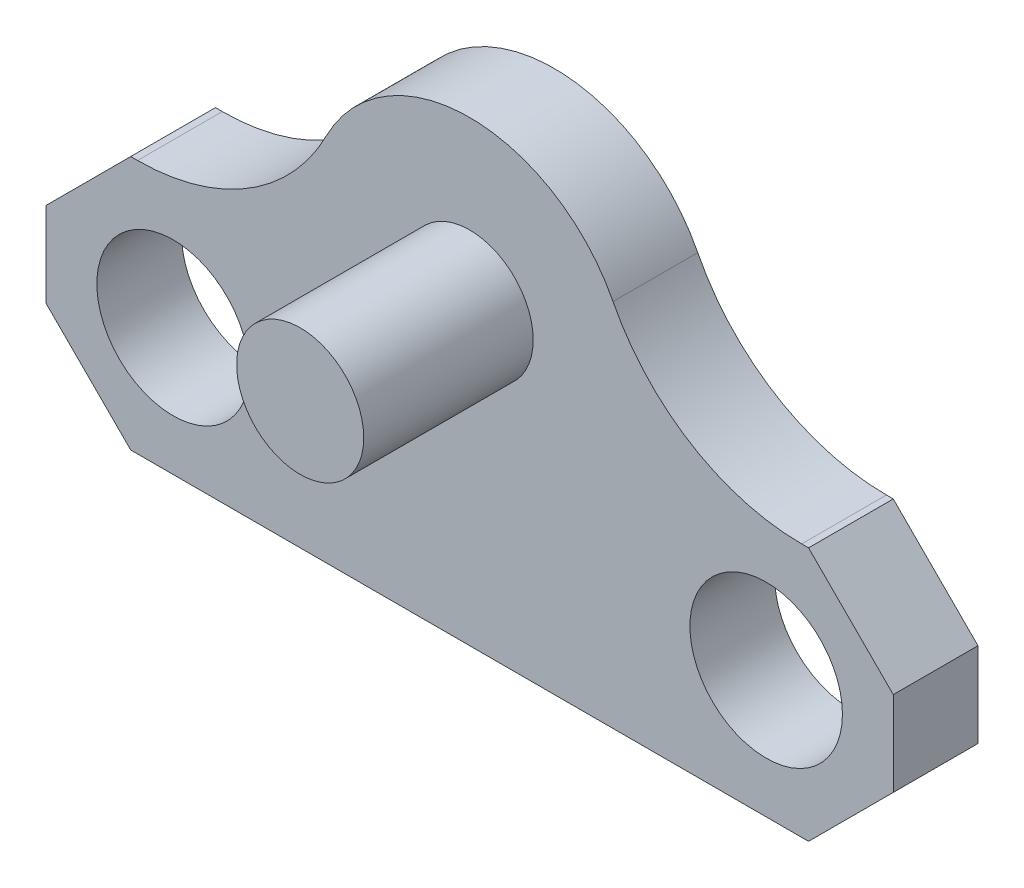
SolidWorks part; units mm, degrees
ref_plane "Front Plane" through (0, 0, 0) normal (0, 0, 1) x (1, 0, 0)
ref_plane "Top Plane" through (0, 0, 0) normal (0, 1, 0) x (1, 0, 0)
ref_plane "Right Plane" through (0, 0, 0) normal (1, 0, 0) x (0, 0, -1)
sketch "Sketch1" plane through (0, 0, 0) normal (0, 0, 1) x (1, 0, 0)
  line L0 (22.6547, 7.62) -> (25.4, 7.62)
  line L1 (0, 0) -> (25.4, 0)
  line L2 (0, 0) -> (0, 7.62)
  line L3 (0, 7.62) -> (2.7453, 7.62)
  line L4 (25.4, 0) -> (25.4, 7.62)
  line L5 (3.81, 3.81) -> (21.59, 3.81) construction
  circle A0 centre (12.7, 8.89) radius 2.286 construction
  arc A1 (16.9986, 11.0836) -> (8.4014, 11.0836) centre (12.7, 8.89) ccw
  arc A2 (2.7453, 7.62) -> (8.4014, 11.0836) centre (2.7453, 13.97) ccw
  arc A3 (16.9986, 11.0836) -> (22.6547, 7.62) centre (22.6547, 13.97) ccw
  circle A4 centre (3.81, 3.81) radius 2.286
  circle A5 centre (21.59, 3.81) radius 2.286
  point P9 (12.7, 0)
  point P18 (12.7, 3.81)
  point P19 (25.4, 3.81)
  dimension "D2" = 2.54
  dimension "D3" = 4.572
  dimension "D5" = 12.7
  dimension "D7" = 3.81
  dimension "D8" = 4.572
  dimension "D6" = 3.81
  dimension "D1" = 25.4
  dimension "D4" = 1.27
  dimension "D9" = 5.08
  dimension "D10" = 17.78
extrude "Boss-Extrude1" add sketch "Sketch1" along normal blind 2.54
sketch "Sketch2" plane through (0, 0, 2.54) normal (0, 0, 1) x (1, 0, 0)
  circle A0 centre (12.7, 8.89) radius 1.905
  arc A1 (16.9986, 11.0836) -> (8.4014, 11.0836) centre (12.7, 8.89) ccw construction
  dimension "D1" = 3.81
extrude "Boss-Extrude2" add sketch "Sketch2" along normal blind 5.08
chamfer "Chamfer1" distance 2.54 angle 45 4 edges at (25.4, 7.62, 1.27) (0, 7.62, 1.27) (0, 0, 1.27) (25.4, 0, 1.27)
